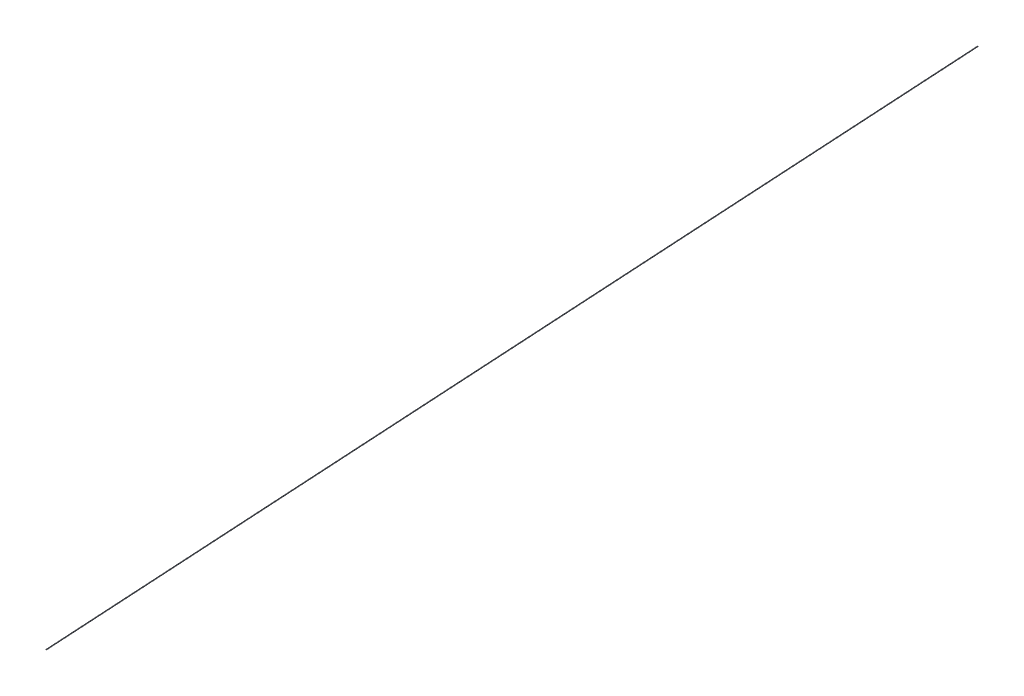
SolidWorks part; units mm, degrees
ref_plane "Front Plane" through (0, 0, 0) normal (0, 0, 1) x (1, 0, 0)
ref_plane "Top Plane" through (0, 0, 0) normal (0, 1, 0) x (1, 0, 0)
ref_plane "Right Plane" through (0, 0, 0) normal (1, 0, 0) x (0, 0, -1)
sketch "Sketch1" plane through (0, 0, 0) normal (1, 0, 0) x (0, 0, -1)
  line L0 (0, 0) -> (14101.6, 0) construction
  line L1 (14101.6, 0) -> (14101.6, 857.6) construction
  line L3 (14101.6, 857.6) -> (14091.6, 857.6)
  line L4 (0, 0) -> (10, 0)
  line L5 (10, 0) -> (14091.6, 857.6)
  dimension "D1" = 14101.6
  dimension "D2" = 10
  dimension "D3" = 10
  dimension "D4" = 857.6
sketch "Sketch2" plane through (0, 0, 0) normal (0, 0, 1) x (1, 0, 0)
  circle A0 centre (0, 0) radius 3.8
  dimension "D1" = 7.6
sweep "Sweep1" add profiles "Sketch2" path "Sketch1"
